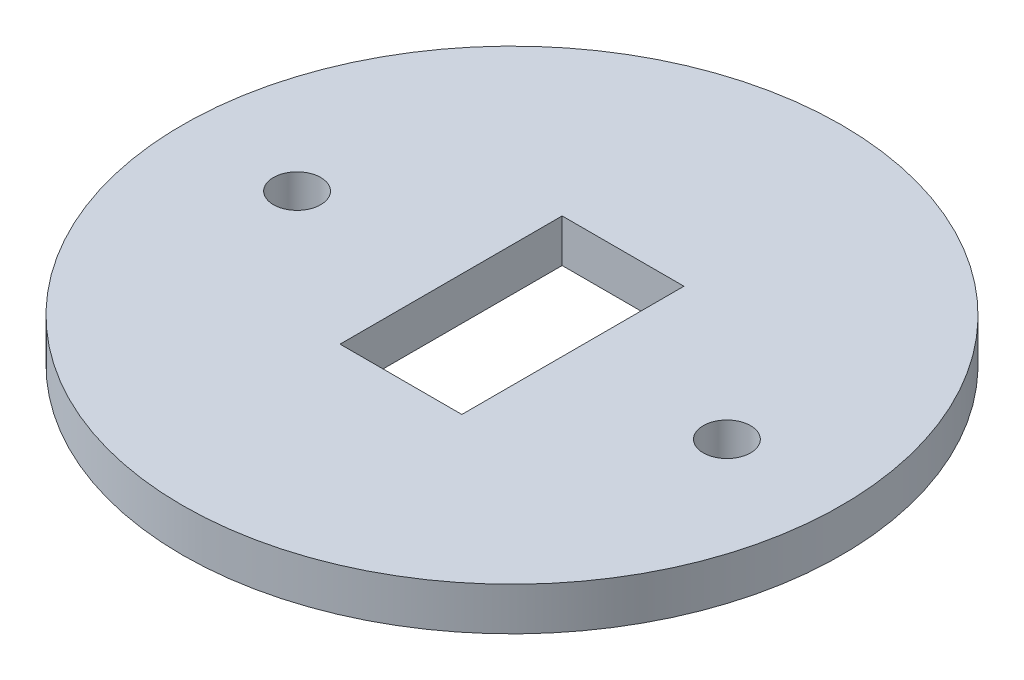
SolidWorks part; units mm, degrees
ref_plane "Front Plane" through (0, 0, 0) normal (0, 0, 1) x (1, 0, 0)
ref_plane "Top Plane" through (0, 0, 0) normal (0, 1, 0) x (1, 0, 0)
ref_plane "Right Plane" through (0, 0, 0) normal (1, 0, 0) x (0, 0, -1)
sketch "Sketch1" plane through (0, 0, 0) normal (0, 1, 0) x (1, 0, 0)
  line L1 (4.25, -7.75) -> (-4.25, -7.75)
  line L2 (4.25, -7.75) -> (4.25, 7.75)
  line L3 (4.25, 7.75) -> (-4.25, 7.75)
  line L4 (-4.25, -7.75) -> (-4.25, 7.75)
  line L5 (4.25, -7.75) -> (-4.25, 7.75) construction
  line L6 (4.25, 7.75) -> (-4.25, -7.75) construction
  circle A0 centre (0, 0) radius 23
  circle A1 centre (-15, 0) radius 1.65
  circle A2 centre (15, 0) radius 1.65
  point P11 (0, 0)
  dimension "D1" = 46
  dimension "D6" = 3.3
  dimension "D2" = 15.5
  dimension "D3" = 8.5
  dimension "D4" = 15
  dimension "D5" = 15
extrude "Boss-Extrude1" add sketch "Sketch1" along normal blind 3
sketch "Sketch2" plane through (0, 3, 0) normal (0, 1, 0) x (1, 0, 0)
  circle A0 centre (0, 4.6656) radius 15
  dimension "D1" = 30
